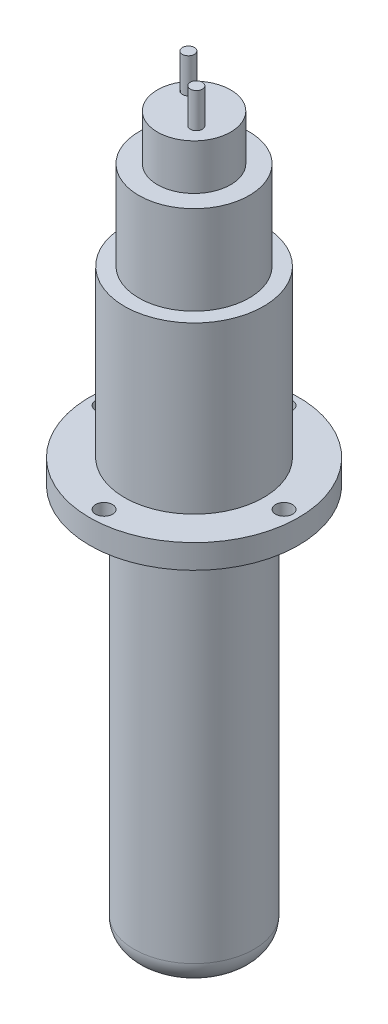
SolidWorks part; units mm, degrees
material "6061 Alloy"
ref_plane "Front" through (0, 0, 0) normal (0, 0, 1) x (1, 0, 0)
ref_plane "Top" through (0, 0, 0) normal (0, 1, 0) x (1, 0, 0)
ref_plane "Right" through (0, 0, 0) normal (1, 0, 0) x (0, 0, -1)
sketch "Sketch1" plane through (0, 0, 0) normal (0, 1, 0) x (1, 0, 0)
  circle A0 centre (0, 0) radius 22.098
  dimension "D1" = 44.196
extrude "Boss-Extrude1" add sketch "Sketch1" along normal blind 5.08
sketch "Sketch2" plane through (0, 5.08, 0) normal (0, 1, 0) x (1, 0, 0)
  circle A0 centre (0, 0) radius 14.732
  dimension "D1" = 29.464
extrude "Boss-Extrude2" add sketch "Sketch2" along normal blind 35.052
sketch "Sketch3" plane through (0, 40.132, 0) normal (0, 1, 0) x (1, 0, 0)
  circle A0 centre (0, 0) radius 11.684
  dimension "D1" = 23.368
extrude "Boss-Extrude3" add sketch "Sketch3" along normal blind 18.796
sketch "Sketch4" plane through (0, 58.928, 0) normal (0, 1, 0) x (1, 0, 0)
  circle A0 centre (0, 0) radius 7.747
  dimension "D1" = 15.494
extrude "Boss-Extrude4" add sketch "Sketch4" along normal blind 9.652
sketch "Sketch5" plane through (0, 68.58, 0) normal (0, 1, 0) x (1, 0, 0)
  circle A0 centre (-4.2434, 3.0444) radius 1.27
  circle A1 centre (2.97, -2.4818) radius 1.27
  dimension "D1" = 2.54
  dimension "D2" = 2.54
extrude "Boss-Extrude5" add sketch "Sketch5" along normal blind 7.366
sketch "Sketch6" plane through (0, 5.08, 0) normal (0, 1, 0) x (1, 0, 0)
  circle A0 centre (0, 19.05) radius 1.7907
  point P2 (0, 19.05)
  dimension "D1" = 3.5814
  dimension "D2" = 19.05
extrude "Cut-Extrude1" cut sketch "Sketch6" against normal blind 7.366
pattern_circular "CirPattern1" count 4 over 360 about axis through (0, 0, 0) along (0, 1, 0) of "Cut-Extrude1"
sketch "Sketch7" plane through (0, 0, 0) normal (0, -1, 0) x (-1, 0, 0)
  circle A0 centre (0, 0) radius 12.7
  dimension "D1" = 25.4
extrude "Boss-Extrude6" add sketch "Sketch7" along normal blind 83.82
fillet "Fillet1" radius 5.08 1 edges at (0, -83.82, -12.7)
